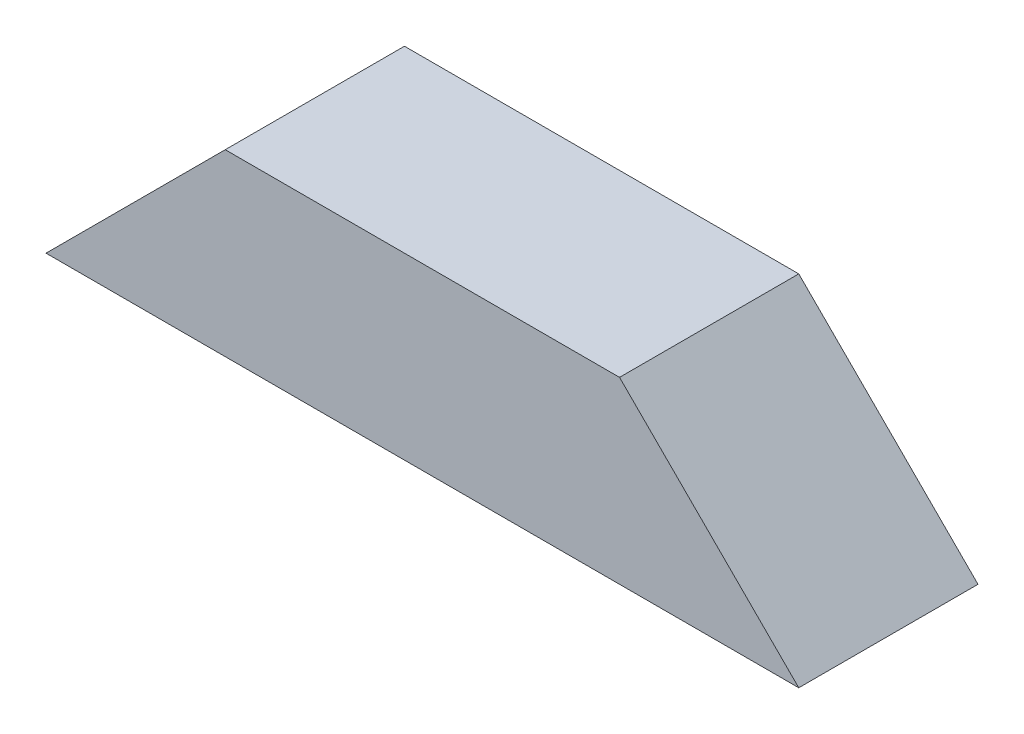
SolidWorks part; units mm, degrees
ref_plane "前视基准面" through (0, 0, 0) normal (0, 0, 1) x (1, 0, 0)
ref_plane "上视基准面" through (0, 0, 0) normal (0, 1, 0) x (1, 0, 0)
ref_plane "右视基准面" through (0, 0, 0) normal (1, 0, 0) x (0, 0, -1)
sketch "草图1" plane through (0, 0, 0) normal (0, 0, 1) x (1, 0, 0)
  line L0 (77.287, 99.8442) -> (161.2871, 99.8442)
  line L1 (97.287, 119.8442) -> (141.2871, 119.8442)
  line L2 (77.287, 99.8442) -> (97.287, 119.8442)
  line L3 (161.2871, 99.8442) -> (141.2871, 119.8442)
  dimension "D1" = 20
  dimension "D2" = 84
extrude "凸台-拉伸1" add sketch "草图1" along normal blind 20
